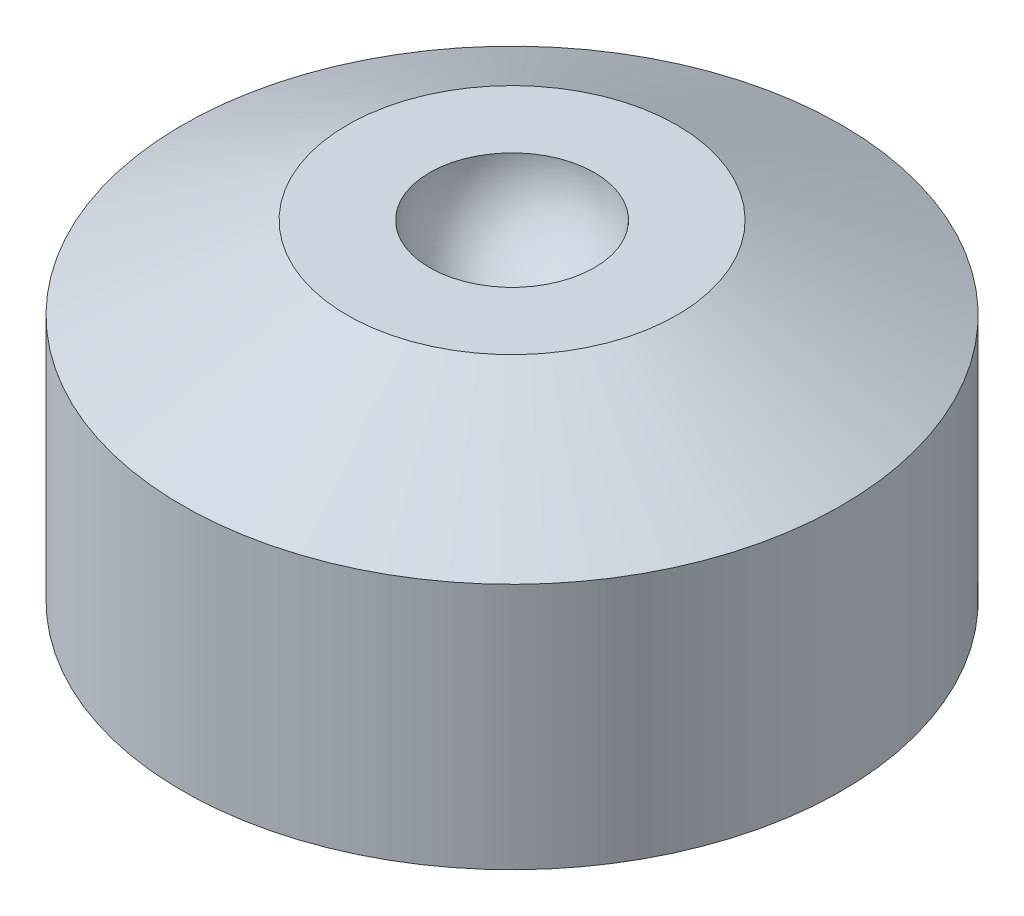
SolidWorks part; units mm, degrees
ref_plane "Front Plane" through (0, 0, 0) normal (0, 0, 1) x (1, 0, 0)
ref_plane "Top Plane" through (0, 0, 0) normal (0, 1, 0) x (1, 0, 0)
ref_plane "Right Plane" through (0, 0, 0) normal (1, 0, 0) x (0, 0, -1)
sketch "Sketch1" plane through (0, 0, 0) normal (1, 0, 0) x (0, 0, -1)
  line L0 (0, 0) -> (0, 27.5729) construction
  line L1 (0, 0) -> (-25.4, 0)
  line L2 (0, 0) -> (0, 9.5488)
  line L4 (-25.4, 0) -> (-25.4, 19.05)
  line L5 (-25.4, 19.05) -> (-12.7, 25.4)
  line L6 (-12.7, 25.4) -> (-6.35, 25.4)
  line L7 (0, 9.5488) -> (0, 19.05)
  arc A0 (-6.35, 25.4) -> (0, 19.05) centre (0, 25.4) ccw
  dimension "D1" = 25.4
  dimension "D3" = 6.35
  dimension "D2" = 19.05
  dimension "D4" = 6.35
  dimension "D5" = 6.35
revolve "Revolve1" add sketch "Sketch1" angle 360 about L0
